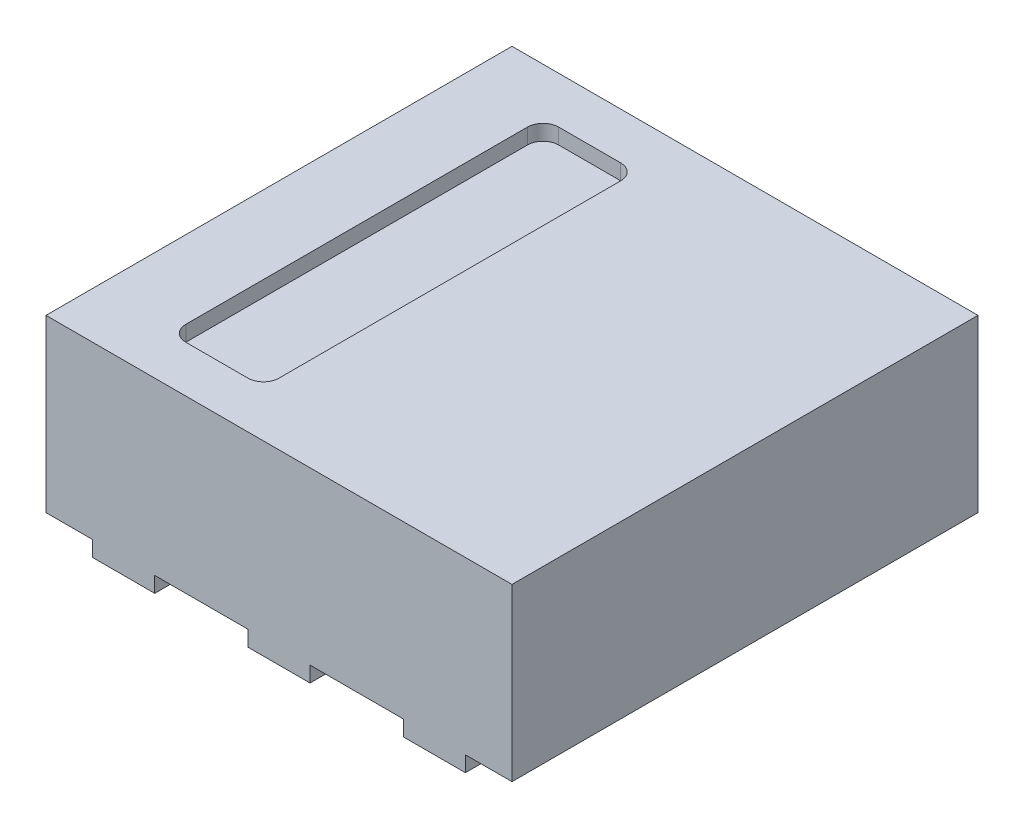
SolidWorks part; units mm, degrees
ref_plane "Спереди" through (0, 0, 0) normal (0, 0, 1) x (1, 0, 0)
ref_plane "Сверху" through (0, 0, 0) normal (0, 1, 0) x (1, 0, 0)
ref_plane "Справа" through (0, 0, 0) normal (1, 0, 0) x (0, 0, -1)
sketch "Эскиз1" plane through (0, 0, 0) normal (0, 1, 0) x (1, 0, 0)
  line L1 (-1.5, 1.5) -> (1.5, 1.5)
  line L2 (-1.5, 1.5) -> (-1.5, -1.5)
  line L3 (-1.5, -1.5) -> (1.5, -1.5)
  line L4 (1.5, 1.5) -> (1.5, -1.5)
  point P4 (-1.5, 0)
  point P6 (0, 1.5)
  dimension "D1" = 3
extrude "Бобышка-Вытянуть1" add sketch "Эскиз1" along normal blind 1.1
sketch "Эскиз2" plane through (0, 1.1, 0) normal (0, 1, 0) x (1, 0, 0)
  line L0 (1.5, -1.5) -> (1.5, 1.5) construction
  line L1 (-0.9, 1.2) -> (-0.5, 1.2)
  line L2 (-1, 1.1) -> (-1, -1.1)
  line L3 (-0.9, -1.2) -> (-0.5, -1.2)
  line L4 (-0.4, 1.1) -> (-0.4, -1.1)
  arc A0 (-0.5, -1.2) -> (-0.4, -1.1) centre (-0.5, -1.1) ccw
  arc A1 (-1, -1.1) -> (-0.9, -1.2) centre (-0.9, -1.1) ccw
  arc A2 (-0.5, 1.2) -> (-0.4, 1.1) centre (-0.5, 1.1) cw
  arc A3 (-0.9, 1.2) -> (-1, 1.1) centre (-0.9, 1.1) ccw
  point P4 (-0.7, -1.2)
  point P7 (-1, 0)
  point P13 (-1, -1.2)
  point P16 (-0.4, 1.2)
  point P19 (-1, 1.2)
  dimension "D4" = 0.1
  dimension "D1" = 2.4
  dimension "D2" = 0.6
  dimension "D3" = 2.2
extrude "Вырез-Вытянуть1" cut sketch "Эскиз2" against normal blind 0.1
sketch "Эскиз3" plane through (0, 0, 0) normal (0, -1, 0) x (1, 0, 0)
  line L0 (-1.5, 1.5) -> (1.5, 1.5) construction
  line L1 (1.2, -0.75) -> (-1.2, -0.75)
  line L2 (1.2, -0.75) -> (1.2, 0.75)
  line L3 (1.2, 0.75) -> (-0.8, 0.75)
  line L4 (-1.2, -0.75) -> (-1.2, 0.35)
  line L5 (1.2, -1.5) -> (0.8, -1.5)
  line L6 (1.2, -1.5) -> (1.2, -1.1)
  line L7 (1.2, -1.1) -> (0.8, -1.1)
  line L8 (0.8, -1.5) -> (0.8, -1.1)
  line L9 (0.2, -1.5) -> (-0.2, -1.5)
  line L10 (0.2, -1.5) -> (0.2, -1.1)
  line L11 (0.2, -1.1) -> (-0.2, -1.1)
  line L12 (-0.2, -1.5) -> (-0.2, -1.1)
  line L13 (-0.8, -1.5) -> (-1.2, -1.5)
  line L14 (-0.8, -1.5) -> (-0.8, -1.1)
  line L15 (-0.8, -1.1) -> (-1.2, -1.1)
  line L16 (-1.2, -1.5) -> (-1.2, -1.1)
  line L17 (1.2, 1.1) -> (0.8, 1.1)
  line L18 (1.2, 1.1) -> (1.2, 1.5)
  line L19 (1.2, 1.5) -> (0.8, 1.5)
  line L20 (0.8, 1.1) -> (0.8, 1.5)
  line L21 (0.2, 1.1) -> (-0.2, 1.1)
  line L22 (0.2, 1.1) -> (0.2, 1.5)
  line L23 (0.2, 1.5) -> (-0.2, 1.5)
  line L24 (-0.2, 1.1) -> (-0.2, 1.5)
  line L25 (1.5, -1.5) -> (-1.5, -1.5) construction
  line L26 (-0.8, 1.1) -> (-1.2, 1.1)
  line L27 (-0.8, 1.1) -> (-0.8, 1.5)
  line L28 (-0.8, 1.5) -> (-1.2, 1.5)
  line L29 (-1.2, 1.1) -> (-1.2, 1.5)
  line L30 (0, -1.5) -> (0, 1.5) construction
  line L31 (-1.2, 0.35) -> (-0.8, 0.75)
  point P1 (1.2, 0)
  point P30 (1, -1.5)
  point P33 (0, -1.5)
  point P34 (-1, -1.5)
  point P35 (1, 1.5)
  point P38 (0, -0.75)
  point P41 (0, 1.5)
  point P42 (0, 1.5)
  point P43 (-1, 1.5)
  point P44 (0, -1.5)
  dimension "D1" = 0.4
  dimension "D2" = 1
  dimension "D3" = 2.4
  dimension "D4" = 1.5
  dimension "D5" = 135
  dimension "D6" = 1.1
extrude "Бобышка-Вытянуть2" add sketch "Эскиз3" along normal blind 0.1
